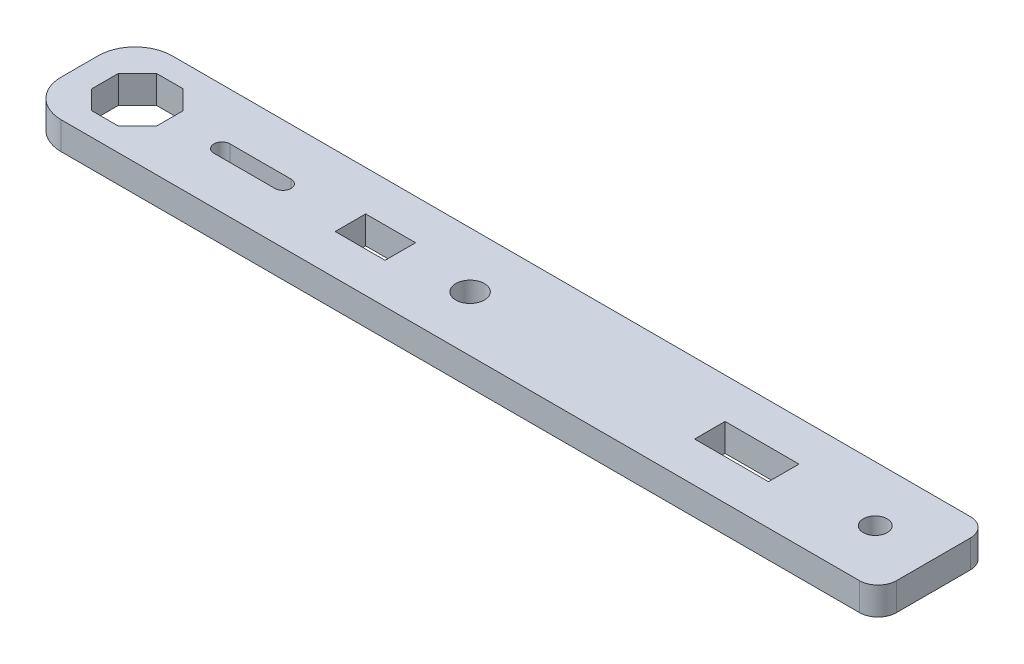
SolidWorks part; units mm, degrees
ref_plane "Front Plane" through (0, 0, 0) normal (0, 0, 1) x (1, 0, 0)
ref_plane "Top Plane" through (0, 0, 0) normal (0, 1, 0) x (1, 0, 0)
ref_plane "Right Plane" through (0, 0, 0) normal (1, 0, 0) x (0, 0, -1)
sketch "Sketch2" plane through (0, 0, 0) normal (0, 1, 0) x (1, 0, 0)
  line L1 (0, 0) -> (92.4, 0)
  line L2 (0, 0) -> (0, 12)
  line L3 (0, 12) -> (92.4, 12)
  line L4 (92.4, 0) -> (92.4, 12)
  dimension "D1" = 92.4
  dimension "D2" = 12
extrude "Boss-Extrude1" add sketch "Sketch2" along normal blind 3
fillet "Fillet1" radius 4 2 edges at (0, 1.5, -12) (0, 1.5, 0)
fillet "Fillet2" radius 2 2 edges at (92.4, 1.5, -12) (92.4, 1.5, 0)
sketch "Sketch3" plane through (0, 3, 0) normal (0, 1, 0) x (1, 0, 0)
  line L0 (15.4, 6) -> (22, 6) construction
  line L1 (9.75, 7.4497) -> (7.6997, 9.5)
  line L2 (7.6997, 9.5) -> (4.8003, 9.5)
  line L3 (4.8003, 9.5) -> (2.75, 7.4497)
  line L4 (2.75, 7.4497) -> (2.75, 4.5503)
  line L5 (2.75, 4.5503) -> (4.8003, 2.5)
  line L6 (4.8003, 2.5) -> (7.6997, 2.5)
  line L7 (7.6997, 2.5) -> (9.75, 4.5503)
  line L8 (9.75, 4.5503) -> (9.75, 7.4497)
  line L9 (15.4, 6.875) -> (22, 6.875)
  line L10 (15.4, 5.125) -> (22, 5.125)
  line L11 (0, 6) -> (92.4, 6) construction
  line L12 (29.3, 7.5) -> (34.7, 7.5)
  line L13 (29.3, 7.5) -> (29.3, 4.5)
  line L14 (29.3, 4.5) -> (34.7, 4.5)
  line L15 (34.7, 7.5) -> (34.7, 4.5)
  line L16 (68.2, 7.5) -> (76.2, 7.5)
  line L17 (68.2, 7.5) -> (68.2, 4.5)
  line L18 (68.2, 4.5) -> (76.2, 4.5)
  line L19 (76.2, 7.5) -> (76.2, 4.5)
  line L20 (0, 8) -> (0, 4) construction
  line L21 (92.4, 2) -> (92.4, 10) construction
  circle A0 centre (6.25, 6) radius 3.7884 construction
  arc A1 (15.4, 6.875) -> (15.4, 5.125) centre (15.4, 6) ccw
  arc A2 (22, 5.125) -> (22, 6.875) centre (22, 6) ccw
  circle A3 centre (42.25, 6) radius 1.55
  circle A4 centre (86.1, 6) radius 1.3
  point P12 (18.7, 6)
  point P35 (0, 0)
  point P36 (29.3, 6)
  point P37 (42.2423, 6)
  point P38 (68.2, 6)
  point P39 (88.7558, 6)
  dimension "D1" = 3.1
  dimension "D2" = 2.6
  dimension "D4" = 6.6
  dimension "D3" = 7
  dimension "D5" = 1.75
  dimension "D6" = 5.4
  dimension "D7" = 3
  dimension "D8" = 8
  dimension "D9" = 6.3
  dimension "D10" = 16.2
  dimension "D11" = 42.25
  dimension "D12" = 29.3
  dimension "D13" = 15.4
  dimension "D14" = 2.75
extrude "Cut-Extrude1" cut sketch "Sketch3" against normal through all
sketch "Sketch4" plane through (0, 3, 0) normal (0, 1, 0) x (1, 0, 0)
  line L0 (34.7, 4.5) -> (34.7, 7.5) construction
  line L1 (29.3, 7.5) -> (34.7, 7.5)
  line L2 (29.3, 7.5) -> (29.3, 7.65)
  line L3 (29.3, 7.65) -> (34.7, 7.65)
  line L4 (34.7, 7.5) -> (34.7, 7.65)
  line L5 (29.3, 4.5) -> (34.7, 4.5)
  line L6 (29.3, 4.5) -> (29.3, 4.35)
  line L7 (29.3, 4.35) -> (34.7, 4.35)
  line L8 (34.7, 4.5) -> (34.7, 4.35)
  line L9 (76.2, 7.5) -> (68.2, 7.5)
  line L10 (76.2, 7.5) -> (76.2, 7.65)
  line L11 (76.2, 7.65) -> (68.2, 7.65)
  line L12 (68.2, 7.5) -> (68.2, 7.65)
  line L13 (76.2, 4.5) -> (68.2, 4.5)
  line L14 (76.2, 4.5) -> (76.2, 4.35)
  line L15 (76.2, 4.35) -> (68.2, 4.35)
  line L16 (68.2, 4.5) -> (68.2, 4.35)
  line L17 (68.2, 7.5) -> (68.2, 4.5) construction
  dimension "D1" = 0.15
extrude "Cut-Extrude2" cut sketch "Sketch4" against normal through all
